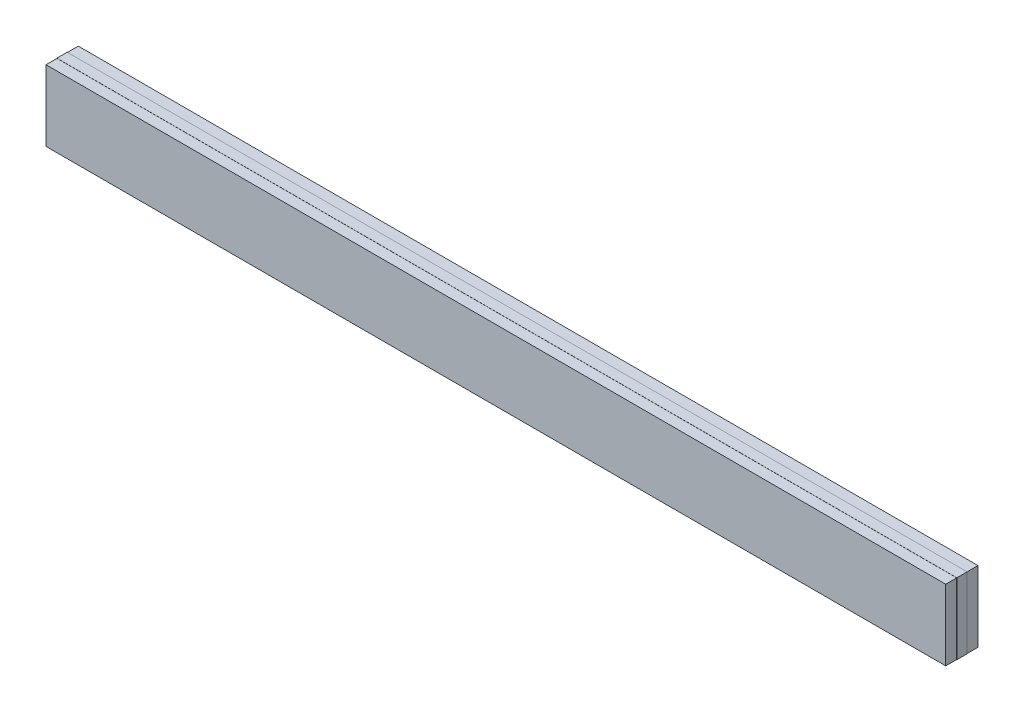
SolidWorks part; units mm, degrees
ref_plane "Front Plane" through (0, 0, 0) normal (0, 0, 1) x (1, 0, 0)
ref_plane "Top Plane" through (0, 0, 0) normal (0, 1, 0) x (1, 0, 0)
ref_plane "Right Plane" through (0, 0, 0) normal (1, 0, 0) x (0, 0, -1)
sketch "Sketch1" plane through (0, 0, 0) normal (0, 0, 1) x (1, 0, 0)
  line L1 (-34.85, 2.75) -> (34.85, 2.75)
  line L2 (-34.85, 2.75) -> (-34.85, -2.75)
  line L3 (-34.85, -2.75) -> (34.85, -2.75)
  line L4 (34.85, 2.75) -> (34.85, -2.75)
  line L5 (-34.85, 2.75) -> (34.85, -2.75) construction
  line L6 (-34.85, -2.75) -> (34.85, 2.75) construction
  point P0 (0, 0)
  dimension "D1" = 5.5
  dimension "D2" = 69.7
extrude "Boss-Extrude1" add sketch "Sketch1" along normal mid plane 0.8
sketch "Sketch2" plane through (0, 0, 0.4) normal (0, 0, 1) x (1, 0, 0)
  line L8 (34.84, -2.74) -> (34.84, 2.74)
  line L9 (34.84, 2.74) -> (-34.84, 2.74)
  line L10 (-34.84, 2.74) -> (-34.84, -2.74)
  line L11 (-34.84, -2.74) -> (34.84, -2.74)
  line L12 (34.84, -2.74) -> (34.84, 2.74)
  line L13 (34.84, 2.74) -> (-34.84, 2.74)
  line L14 (-34.84, 2.74) -> (-34.84, -2.74)
  line L15 (-34.84, -2.74) -> (34.84, -2.74)
  dimension "D1" = 0.01
extrude "Boss-Extrude2" add sketch "Sketch2" along normal blind 0.85
sketch "Sketch3" plane through (0, 0, -0.4) normal (0, 0, -1) x (-1, 0, 0)
  line L8 (-34.84, 2.74) -> (-34.84, -2.74)
  line L9 (-34.84, -2.74) -> (34.84, -2.74)
  line L10 (34.84, -2.74) -> (34.84, 2.74)
  line L11 (34.84, 2.74) -> (-34.84, 2.74)
  line L12 (-34.84, 2.74) -> (-34.84, -2.74)
  line L13 (-34.84, -2.74) -> (34.84, -2.74)
  line L14 (34.84, -2.74) -> (34.84, 2.74)
  line L15 (34.84, 2.74) -> (-34.84, 2.74)
  dimension "D1" = 0.01
extrude "Boss-Extrude3" add sketch "Sketch3" along normal blind 0.85
